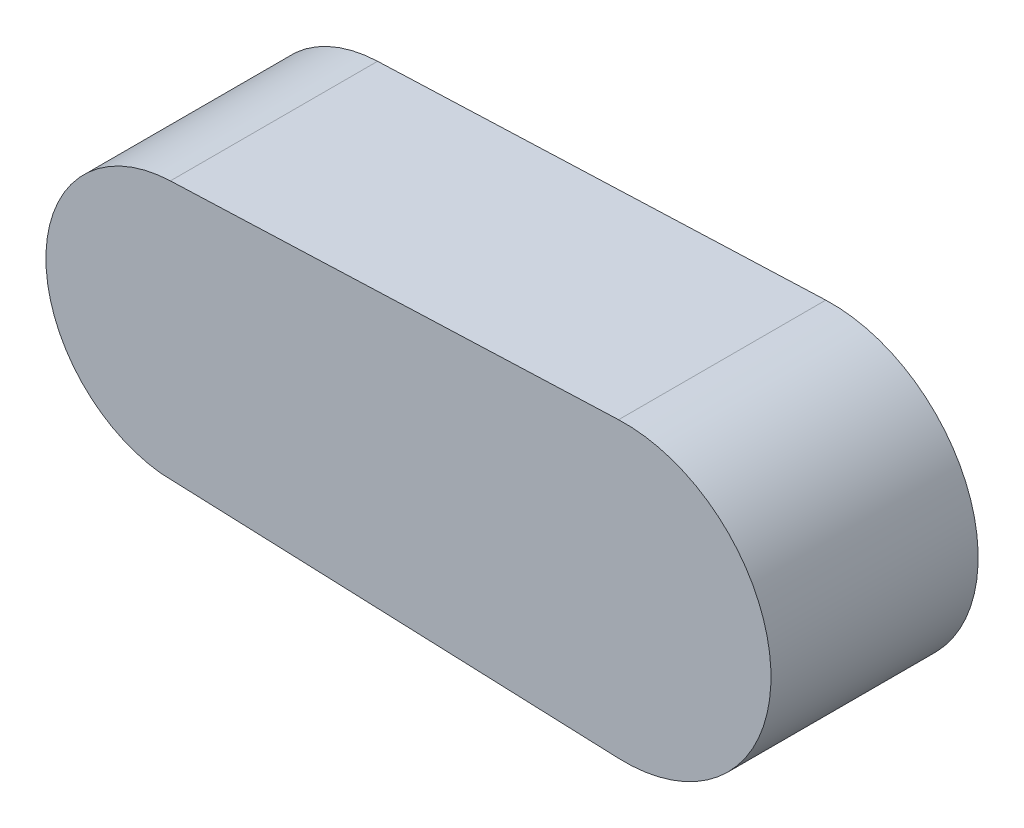
SolidWorks part; units mm, degrees
ref_plane "Front Plane" through (0, 0, 0) normal (0, 0, 1) x (1, 0, 0)
ref_plane "Top Plane" through (0, 0, 0) normal (0, 1, 0) x (1, 0, 0)
ref_plane "Right Plane" through (0, 0, 0) normal (1, 0, 0) x (0, 0, -1)
sketch "Sketch1" plane through (0, 0, 0) normal (0, 0, 1) x (1, 0, 0)
  line L0 (-137.8846, 74.9445) -> (121.7308, 84.9371)
  line L1 (-210, 85) -> (210, 85) construction
  line L2 (-210, 85) -> (-210, -85) construction
  line L3 (-210, -85) -> (210, -85) construction
  line L4 (210, 85) -> (210, -85) construction
  line L5 (-143.4294, -74.5248) -> (121.6648, -84.9345)
  arc A0 (121.6648, -84.9345) -> (121.7308, 84.9371) centre (125, 0) ccw
  arc A1 (-137.8846, 74.9445) -> (-143.4294, -74.5248) centre (-135, 0) ccw
  point P4 (0, 85)
  point P6 (210, 0)
  dimension "D3" = 150
  dimension "D1" = 420
  dimension "D2" = 170
extrude "Extrude1" add sketch "Sketch1" along normal blind 120
